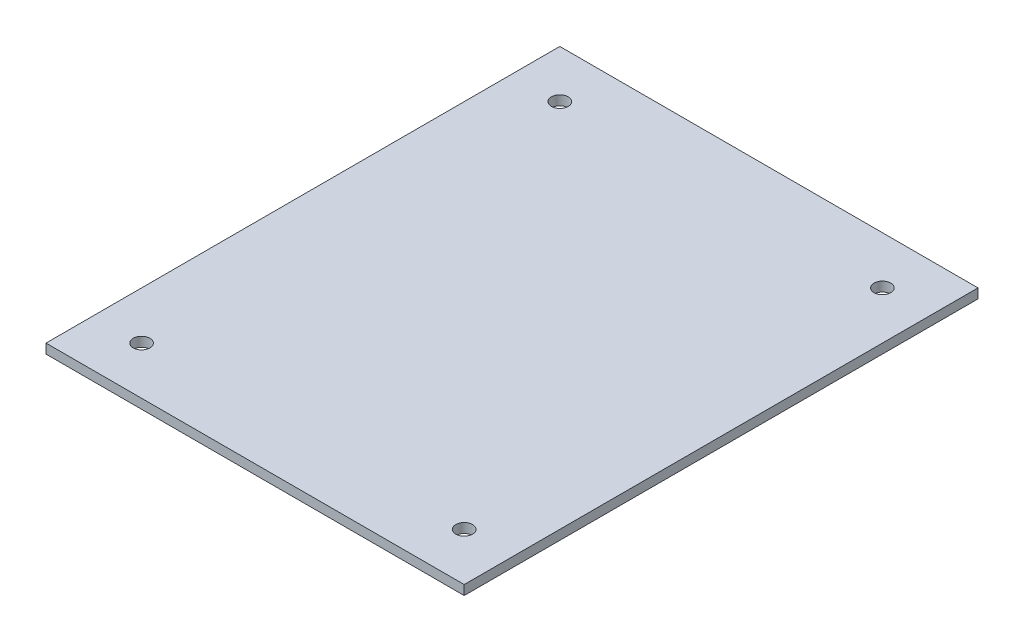
SolidWorks part; units mm, degrees
ref_plane "Front Plane" through (0, 0, 0) normal (0, 0, 1) x (1, 0, 0)
ref_plane "Top Plane" through (0, 0, 0) normal (0, 1, 0) x (1, 0, 0)
ref_plane "Right Plane" through (0, 0, 0) normal (1, 0, 0) x (0, 0, -1)
sketch "Sketch1" plane through (0, 0, 0) normal (0, 1, 0) x (1, 0, 0)
  line L1 (0, 205) -> (175, 205)
  line L2 (0, 205) -> (0, -10)
  line L3 (0, -10) -> (175, -10)
  line L4 (175, 205) -> (175, -10)
  circle A0 centre (20, 10) radius 3.5
  circle A1 centre (155, 10) radius 3.5
  circle A3 centre (20, 185) radius 3.5
  circle A5 centre (155, 185) radius 3.5
  point P8 (0, 0)
  point P9 (0, 0)
  point P10 (0, 0)
extrude "Boss-Extrude1" add sketch "Sketch1" along normal blind 4
